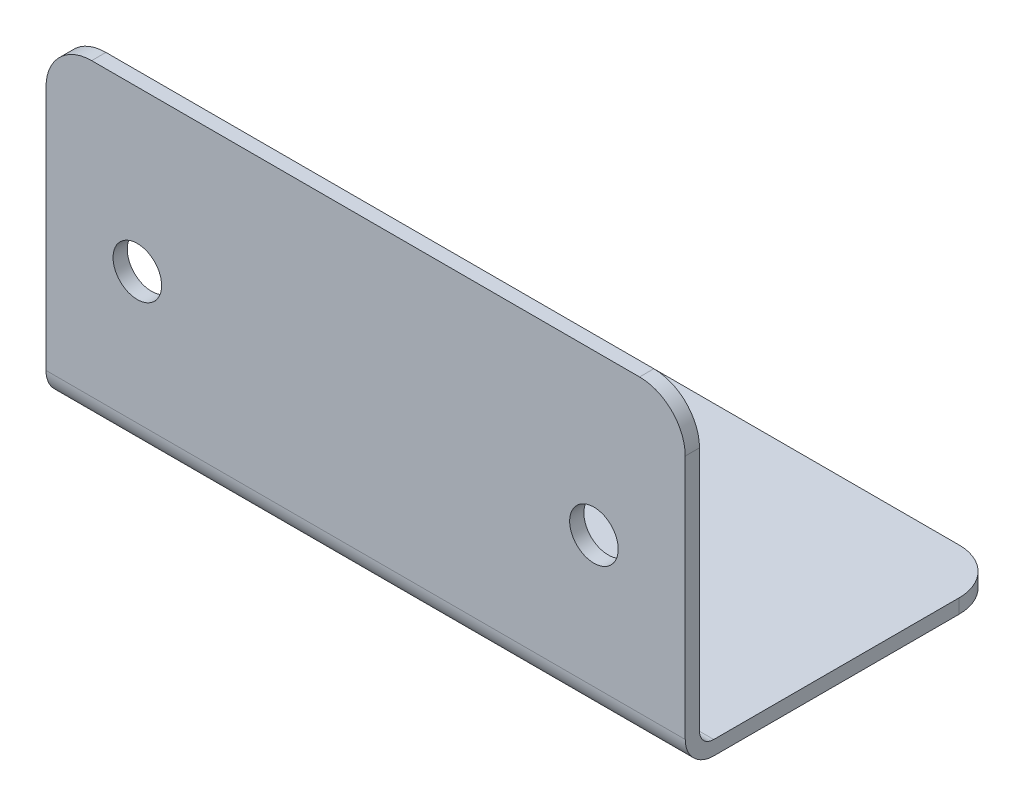
SolidWorks part; units mm, degrees
material "Galvanized Steel"
ref_plane "Front Plane" through (0, 0, 0) normal (0, 0, 1) x (1, 0, 0)
ref_plane "Top Plane" through (0, 0, 0) normal (0, 1, 0) x (1, 0, 0)
ref_plane "Right Plane" through (0, 0, 0) normal (1, 0, 0) x (0, 0, -1)
sketch "Sketch1" plane through (0, 0, 0) normal (1, 0, 0) x (0, 0, -1)
  line L0 (0, 44.45) -> (0, 0)
  line L1 (0, 0) -> (44.45, 0)
  line L2 (44.45, 0) -> (44.45, 1.9812)
  line L3 (44.45, 1.9812) -> (1.9812, 1.9812)
  line L4 (1.9812, 1.9812) -> (1.9812, 44.45)
  line L5 (1.9812, 44.45) -> (0, 44.45)
  point P3 (44.45, 3.9883)
  dimension "D1" = 44.45
  dimension "D2" = 1.9812
extrude "Boss-Extrude1" add sketch "Sketch1" along normal blind 88.9
fillet "Fillet1" radius 1.9812 1 edges at (44.45, 1.9812, -1.9812)
fillet "Fillet2" radius 3.9624 1 edges at (44.45, 0, 0)
fillet "Fillet3" radius 6.35 4 edges at (0, 0.9906, -44.45) (88.9, 0.9906, -44.45) (88.9, 44.45, -0.9906) (0, 44.45, -0.9906)
sketch "Sketch2" plane through (0, 0, 0) normal (0, 0, 1) x (1, 0, 0)
  line L0 (88.9, 0) -> (0, 0) construction
  line L1 (0, 38.1) -> (0, 3.9624) construction
  circle A0 centre (12.7, 22.225) radius 3.3782
  circle A1 centre (76.2, 22.225) radius 3.3782
  point P8 (0, 0)
  dimension "D1" = 22.225
  dimension "D4" = 6.7564
  dimension "D2" = 12.7
  dimension "D3" = 63.5
extrude "Cut-Extrude1" cut sketch "Sketch2" against normal blind 88.9
